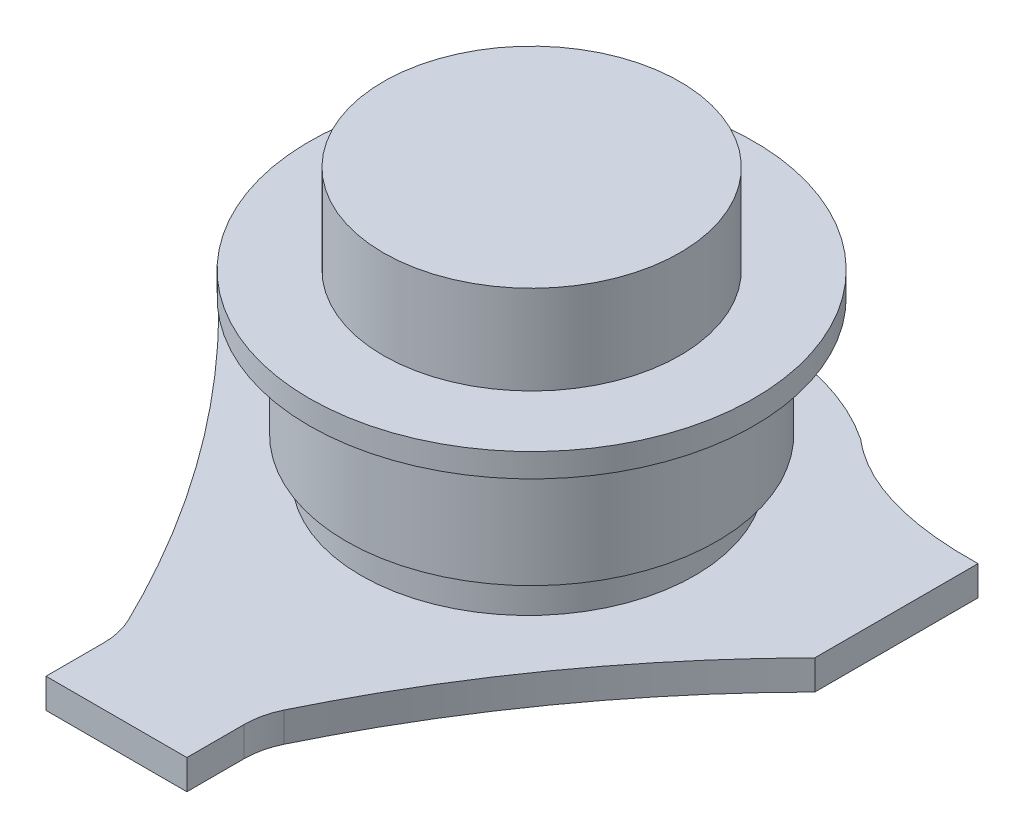
SolidWorks part; units mm, degrees
ref_plane "Front Plane" through (0, 0, 0) normal (0, 0, 1) x (1, 0, 0)
ref_plane "Top Plane" through (0, 0, 0) normal (0, 1, 0) x (1, 0, 0)
ref_plane "Right Plane" through (0, 0, 0) normal (1, 0, 0) x (0, 0, -1)
sketch "Sketch1" plane through (0, 0, 0) normal (0, 1, 0) x (1, 0, 0)
  line L0 (0, 0) -> (0, 25.4) construction
  line L1 (0, 25.4) -> (-67.3263, 25.4) construction
  line L2 (51.054, 0) -> (51.054, 25.4)
  line L3 (-51.054, 0) -> (-51.054, 25.4)
  line L4 (0, 0) -> (0, -2.54)
  line L5 (-51.054, 0) -> (-51.054, -2.54)
  line L6 (51.054, 0) -> (51.054, -2.54)
  line L7 (0, 0) -> (0, -2.54)
  line L8 (12.065, -71.12) -> (-12.065, -71.12)
  line L10 (-12.065, -58.42) -> (-12.065, -71.12)
  line L11 (12.065, -58.42) -> (12.065, -71.12)
  arc A0 (-34.5039, -21.473) -> (-30.5529, -26.7979) centre (0, 0) ccw
  arc A1 (25.874, 31.3392) -> (-25.874, 31.3392) centre (0, 0) ccw
  arc A2 (30.5529, -26.7979) -> (34.5039, -21.473) centre (0, 0) ccw
  spline S0 degree 2 poles (-51.054, -2.54) (-26.746, -27.0772) (-12.065, -58.42) knots 0 0 0 1 1 1
  spline S1 degree 2 poles (51.054, -2.54) (26.746, -27.0772) (12.065, -58.42) knots 0 0 0 1 1 1
  spline S2 degree 2 poles (-51.054, 25.4) (-32.8121, 25.0303) (-22.5628, 33.8013) knots 0 0 0 0.488429 0.488429 0.488429
  spline S3 degree 2 poles (51.054, 25.4) (32.8121, 25.0303) (22.5628, 33.8013) knots 0 0 0 0.488429 0.488429 0.488429
  point P19 (0, -71.12)
  dimension "D1" = 81.28
  dimension "D2" = 25.4
  dimension "D5" = 2.54
  dimension "D9" = 24.13
  dimension "D3" = 51.054
  dimension "D4" = 51.054
  dimension "D6" = 51.054
  dimension "D7" = 51.054
extrude "Boss-Extrude1" add sketch "Sketch1" along normal blind 5.08
fillet "Fillet1" radius 12.7 1 edges at (-12.065, 2.54, 58.42)
fillet "Fillet2" radius 12.7 1 edges at (12.065, 2.54, 58.42)
sketch "Sketch2" plane through (0, 5.08, 0) normal (0, 1, 0) x (1, 0, 0)
  line L0 (0, 40.64) -> (0, 27.94)
  line L1 (0, 0) -> (0, 13.1135) construction
  arc A0 (22.5628, 33.8013) -> (-22.5628, 33.8013) centre (0, 0) ccw construction
  arc A1 (22.5628, 33.8013) -> (-22.5628, 33.8013) centre (0, 0) ccw
  circle A2 centre (0, -0.635) radius 28.575
  point P7 (0, 0)
  point P11 (0, 0)
  dimension "D2" = 57.15
  dimension "D1" = 12.7
extrude "Boss-Extrude2" add sketch "Sketch2" along normal blind 6.35 contours L1 A2 | A2 L1
sketch "Sketch3" plane through (0, 11.43, 0) normal (0, 1, 0) x (1, 0, 0)
  circle A0 centre (0, 0) radius 31.75
  dimension "D1" = 63.5
extrude "Boss-Extrude3" add sketch "Sketch3" along normal blind 20.32
sketch "Sketch4" plane through (0, 31.75, 0) normal (0, 1, 0) x (1, 0, 0)
  circle A0 centre (0, 0) radius 38.1
  dimension "D1" = 76.2
extrude "Boss-Extrude4" add sketch "Sketch4" along normal blind 4.064
sketch "Sketch5" plane through (0, 35.814, 0) normal (0, 1, 0) x (1, 0, 0)
  circle A0 centre (0, 0) radius 25.4
  dimension "D1" = 50.8
extrude "Boss-Extrude5" add sketch "Sketch5" along normal blind 15.24
